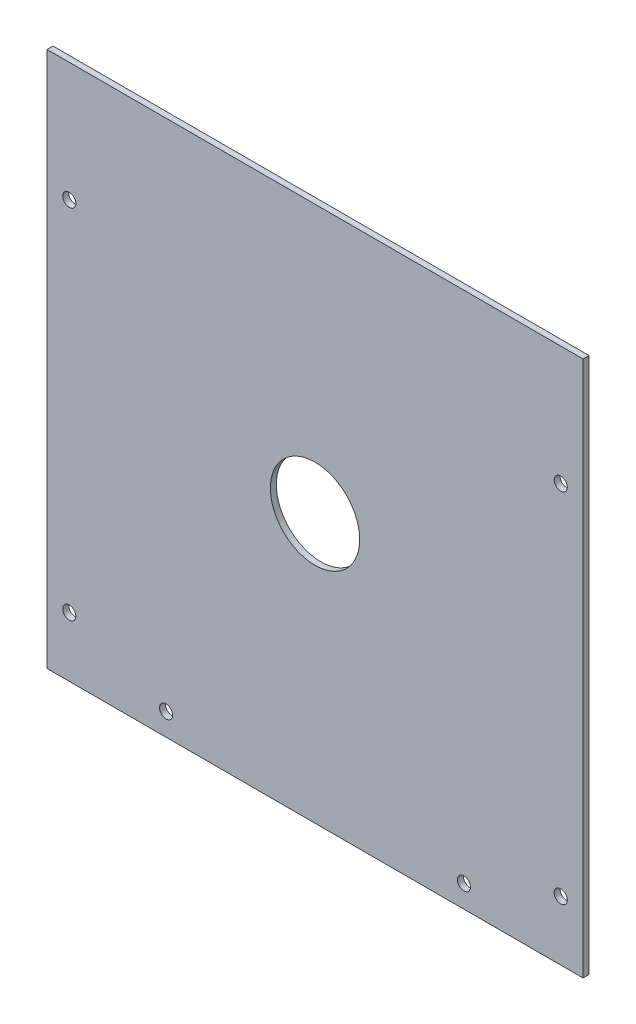
SolidWorks part; units mm, degrees
ref_plane "正面" through (0, 0, 0) normal (0, 0, 1) x (1, 0, 0)
ref_plane "平面" through (0, 0, 0) normal (0, 1, 0) x (1, 0, 0)
ref_plane "右側面" through (0, 0, 0) normal (1, 0, 0) x (0, 0, -1)
sketch "ｽｹｯﾁ1" plane through (0, 0, 0) normal (0, 0, 1) x (1, 0, 0)
  line L1 (-90, 90) -> (90, 90)
  line L2 (-90, 90) -> (-90, -90)
  line L3 (-90, -90) -> (90, -90)
  line L4 (90, 90) -> (90, -90)
  line L5 (-90, 90) -> (90, -90) construction
  line L6 (-90, -90) -> (90, 90) construction
  point P0 (0, 0)
  dimension "D1" = 180
  dimension "D2" = 180
extrude "ﾎﾞｽ - 押し出し1" add sketch "ｽｹｯﾁ1" along normal blind 2
sketch "ｽｹｯﾁ2" plane through (0, 0, 2) normal (0, 0, 1) x (1, 0, 0)
  circle A0 centre (0, 0) radius 15
  dimension "D1" = 30
extrude "ｶｯﾄ - 押し出し1" cut sketch "ｽｹｯﾁ2" against normal blind 2
sketch "ｽｹｯﾁ3" plane through (0, 0, 0) normal (0, 0, -1) x (-1, 0, 0)
  line L1 (-90, -90) -> (-50, -90)
  line L2 (-90, -90) -> (-90, -82.5)
  line L3 (-90, -82.5) -> (-50, -82.5)
  line L4 (-50, -90) -> (-50, -82.5)
  line L5 (90, -90) -> (50, -90)
  line L6 (90, -90) -> (90, -82.5)
  line L7 (90, -82.5) -> (50, -82.5)
  line L8 (50, -90) -> (50, -82.5)
  circle A0 centre (-50, -82.5) radius 2.2
  circle A1 centre (50, -82.5) radius 2.2
  dimension "D5" = 4.4
  dimension "D6" = 4.4
  dimension "D1" = 40
  dimension "D2" = 40
  dimension "D3" = 7.5
  dimension "D4" = 7.5
extrude "ｶｯﾄ - 押し出し2" cut sketch "ｽｹｯﾁ3" against normal through all contours L4 A0 L3 | L3 A0 L4 | L7 A1 L8 | L8 A1 L7
sketch "ｽｹｯﾁ4" plane through (0, 0, 0) normal (0, 0, -1) x (-1, 0, 0)
  line L0 (-90, -90) -> (-82.5, -90)
  line L1 (90, -90) -> (-90, -90) construction
  line L2 (-82.5, -90) -> (-82.5, -70)
  line L3 (-82.5, -70) -> (-82.5, 50)
  line L4 (90, -90) -> (82.5, -90)
  line L5 (82.5, -90) -> (82.5, -70)
  line L6 (82.5, -70) -> (82.5, 50)
  circle A0 centre (-82.5, -70) radius 2.2
  circle A1 centre (-82.5, 50) radius 2.2
  circle A2 centre (82.5, 50) radius 2.2
  circle A3 centre (82.5, -70) radius 2.2
  dimension "D4" = 4.4
  dimension "D5" = 4.4
  dimension "D9" = 4.4
  dimension "D10" = 4.4
  dimension "D1" = 20
  dimension "D2" = 120
  dimension "D3" = 7.5
  dimension "D6" = 7.5
  dimension "D7" = 20
  dimension "D8" = 120
extrude "ｶｯﾄ - 押し出し3" cut sketch "ｽｹｯﾁ4" against normal blind 160
